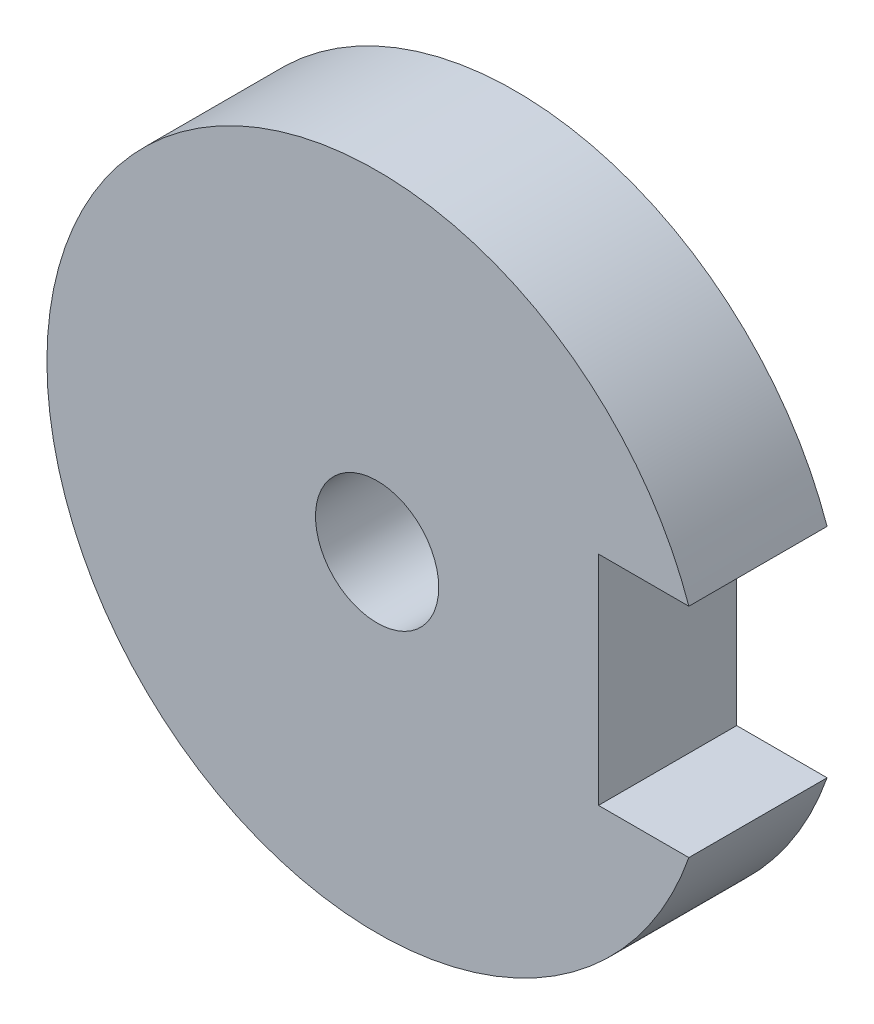
SolidWorks part; units mm, degrees
ref_plane "Front Plane" through (0, 0, 0) normal (0, 0, 1) x (1, 0, 0)
ref_plane "Top Plane" through (0, 0, 0) normal (0, 1, 0) x (1, 0, 0)
ref_plane "Right Plane" through (0, 0, 0) normal (1, 0, 0) x (0, 0, -1)
sketch "Sketch1" plane through (0, 0, 0) normal (0, 0, 1) x (1, 0, 0)
  circle A0 centre (0, 0) radius 1.415
  circle A1 centre (0, 0) radius 7.585
  dimension "D1" = 2.83
  dimension "D2" = 15.17
extrude "Boss-Extrude1" add sketch "Sketch1" along normal blind 3.175
sketch "Sketch2" plane through (0, 0, 3.175) normal (0, 0, 1) x (1, 0, 0)
  line L0 (0, 0) -> (7.585, 0) construction
  line L1 (5.085, -2.5) -> (5.085, 2.5)
  line L2 (5.085, 2.5) -> (7.585, 2.5)
  line L3 (7.585, 2.5) -> (7.585, -2.5)
  line L4 (5.085, -2.5) -> (7.585, -2.5)
  circle A0 centre (0, 0) radius 7.585 construction
  point P6 (5.085, 0)
  point P11 (5.085, 0)
  dimension "D2" = 2.5
  dimension "D3" = 2.5
extrude "Cut-Extrude1" cut sketch "Sketch2" against normal blind 3.175
